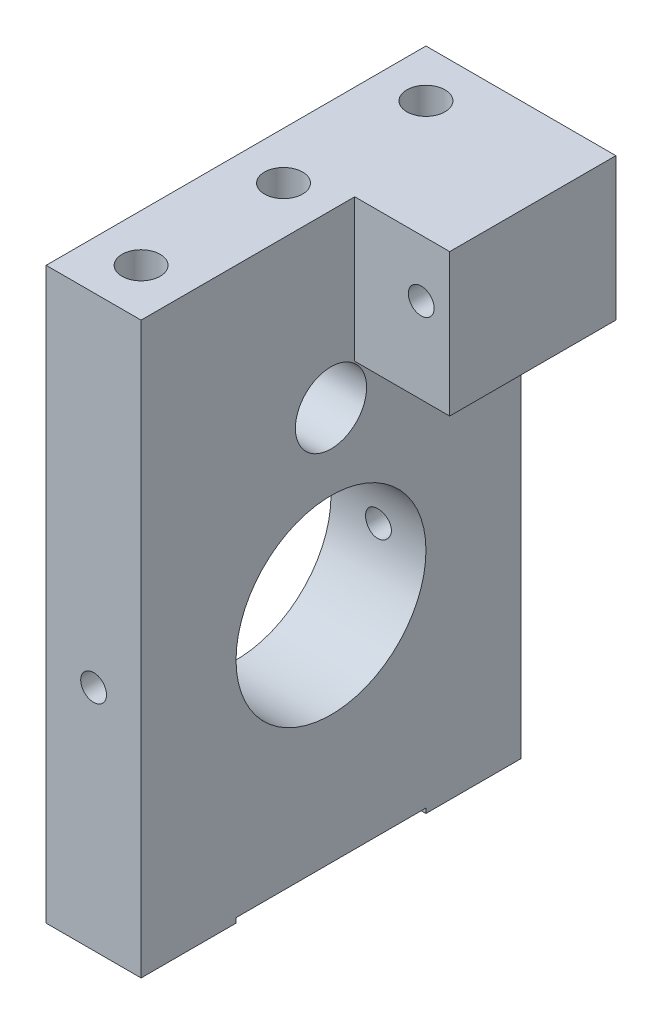
SolidWorks part; units mm, degrees
material "6061 Alloy"
ref_plane "Front Plane" through (0, 0, 0) normal (0, 0, 1) x (1, 0, 0)
ref_plane "Top Plane" through (0, 0, 0) normal (0, 1, 0) x (1, 0, 0)
ref_plane "Right Plane" through (0, 0, 0) normal (1, 0, 0) x (0, 0, -1)
sketch "Sketch1" plane through (0, 0, 0) normal (1, 0, 0) x (0, 0, -1)
  line L1 (-25.4, 38.1) -> (25.4, 38.1)
  line L2 (-25.4, 38.1) -> (-25.4, -38.1)
  line L3 (-25.4, -38.1) -> (25.4, -38.1)
  line L4 (25.4, 38.1) -> (25.4, -38.1)
  dimension "D1" = 25.4
  dimension "D2" = 25.4
  dimension "D3" = 38.1
  dimension "D4" = 38.1
extrude "Boss-Extrude1" add sketch "Sketch1" along normal mid plane 12.7
sketch "Sketch2" plane through (6.35, 0, 0) normal (1, 0, 0) x (0, 0, -1)
  line L1 (25.4, 38.1) -> (3.175, 38.1)
  line L2 (25.4, 38.1) -> (25.4, 19.05)
  line L3 (25.4, 19.05) -> (3.175, 19.05)
  line L4 (3.175, 38.1) -> (3.175, 19.05)
  dimension "D1" = 3.175
  dimension "D2" = 19.05
extrude "Boss-Extrude2" add sketch "Sketch2" along normal blind 12.7
hole_wizard "1/4-20 Tapped Hole1" positions "Sketch4" profile "Sketch3" tap size "1/4-20" standard "ANSI Inch"
sketch "Sketch4" plane through (0, -38.1, 0) normal (0, -1, 0) x (-1, 0, 0)
  point P0 (0, -19.05)
  point P2 (0, 19.05)
  dimension "D1" = 19.05
  dimension "D2" = 19.05
sketch "Sketch3" plane through (0, -38.1, 19.05) normal (1, 0, 0) x (0, 0, -1)
  line L0 (0, 0) -> (0, 20.5838)
  line L1 (0, 20.5838) -> (2.5527, 19.05)
  line L2 (2.5527, 19.05) -> (2.5527, 0)
  line L5 (2.5527, 0) -> (0, 0)
  line L10 (0, 20.5838) -> (-2.5527, 19.05) construction
  line L11 (0, -6.35) -> (0, 107.95) construction
  dimension "Tap Drill Dia." = 5.1054
  dimension "Tap Drill Depth" = 19.05
  dimension "Drill Angle" = 118
cosmetic thread "Hole Thread1" parameters "D1"=12.7, "D2"=6.35
cosmetic thread "Hole Thread2" parameters "D1"=12.7, "D2"=6.35
sketch "Sketch5" plane through (6.35, 0, 0) normal (1, 0, 0) x (0, 0, -1)
  line L0 (-25.4, -38.1) -> (25.4, -38.1) construction
  line L1 (-12.7, -38.1) -> (12.7, -38.1)
  line L2 (-12.7, -38.1) -> (-12.7, -37.465)
  line L3 (-12.7, -37.465) -> (12.7, -37.465)
  line L4 (12.7, -38.1) -> (12.7, -37.465)
  dimension "D1" = 12.7
  dimension "D2" = 12.7
  dimension "D3" = 0.635
extrude "Cut-Extrude1" cut sketch "Sketch5" against normal up to next
hole_wizard "1/4-20 Tapped Hole2" positions "Sketch7" profile "Sketch6" tap size "1/4-20" standard "ANSI Inch"
sketch "Sketch7" plane through (0, 38.1, 0) normal (0, 1, 0) x (1, 0, 0)
  point P0 (0, 19.05)
  point P2 (0, 0)
  point P5 (0, -19.05)
  dimension "D1" = 19.05
  dimension "D2" = 19.05
sketch "Sketch6" plane through (0, 38.1, -19.05) normal (1, 0, 0) x (0, 0, 1)
  line L0 (0, 0) -> (0, 20.5838)
  line L1 (0, 20.5838) -> (2.5527, 19.05)
  line L2 (2.5527, 19.05) -> (2.5527, 0)
  line L5 (2.5527, 0) -> (0, 0)
  line L10 (0, 20.5838) -> (-2.5527, 19.05) construction
  line L11 (0, -6.35) -> (0, 107.95) construction
  dimension "Tap Drill Dia." = 5.1054
  dimension "Tap Drill Depth" = 19.05
  dimension "Drill Angle" = 118
cosmetic thread "Hole Thread3" parameters "D1"=12.7, "D2"=6.35
cosmetic thread "Hole Thread4" parameters "D1"=12.7, "D2"=6.35
cosmetic thread "Hole Thread5" parameters "D1"=12.7, "D2"=6.35
sketch "Sketch8" plane through (6.35, 0, 0) normal (1, 0, 0) x (0, 0, -1)
  line L0 (-25.4, -38.1) -> (-12.7, -38.1) construction
  circle A0 centre (0, -7.62) radius 12.7
  dimension "D1" = 30.48
extrude "Cut-Extrude2" cut sketch "Sketch8" against normal up to next
hole_wizard "#8-32 Tapped Hole1" positions "Sketch10" profile "Sketch9" tap size "#8-32" standard "ANSI Inch" end condition through all
sketch "Sketch10" plane through (0, 0, -3.175) normal (0, 0, 1) x (1, 0, 0)
  line L0 (19.05, 19.05) -> (6.35, 19.05) construction
  line L1 (19.05, 38.1) -> (19.05, 19.05) construction
  point P0 (15.24, 30.48)
  dimension "D1" = 11.43
  dimension "D2" = 3.81
cosmetic thread "Hole Thread6" parameters "D2"=4.1656
sketch "Sketch9" plane through (15.24, 30.48, -3.175) normal (1, 0, 0) x (0, -1, 0)
  line L0 (0, 0) -> (0, 22.225)
  line L1 (0, 22.225) -> (1.7272, 22.225)
  line L2 (1.7272, 22.225) -> (1.7272, 0)
  line L5 (1.7272, 0) -> (0, 0)
  line L11 (0, -6.35) -> (0, 107.95) construction
  dimension "Thru Tap Drill Dia." = 3.4544
  dimension "Thru Tap Drill Depth" = 22.225
sketch "Sketch11" plane through (-6.35, 0, 0) normal (-1, 0, 0) x (0, 0, 1)
  circle A0 centre (0, 15.24) radius 4.7625
  dimension "D1" = 15.24
extrude "Cut-Extrude3" cut sketch "Sketch11" against normal through all
hole_wizard "#8-32 Tapped Hole2" positions "Sketch13" profile "Sketch12" tap size "#8-32" standard "ANSI Inch" end condition through all
sketch "Sketch13" plane through (0, 0, 25.4) normal (0, 0, 1) x (1, 0, 0)
  line L0 (6.35, -38.1) -> (-6.35, -38.1) construction
  point P0 (0, -7.62)
  dimension "D1" = 30.48
sketch "Sketch12" plane through (0, -7.62, 25.4) normal (1, 0, 0) x (0, -1, 0)
  line L0 (0, 0) -> (0, 50.8)
  line L1 (0, 50.8) -> (1.7272, 50.8)
  line L2 (1.7272, 50.8) -> (1.7272, 0)
  line L5 (1.7272, 0) -> (0, 0)
  line L11 (0, -6.35) -> (0, 107.95) construction
  dimension "Thru Tap Drill Dia." = 3.4544
  dimension "Thru Tap Drill Depth" = 50.8
cosmetic thread "Hole Thread7" parameters "D2"=4.1656
